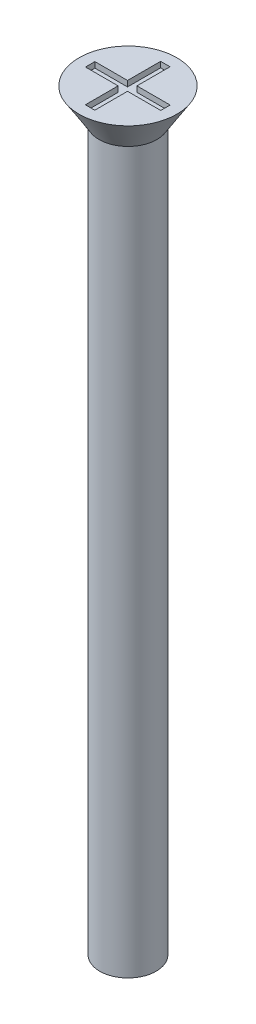
SolidWorks part; units mm, degrees
material "AISI 304"
ref_plane "Front" through (0, 0, 0) normal (0, 0, 1) x (1, 0, 0)
ref_plane "Top" through (0, 0, 0) normal (0, 1, 0) x (1, 0, 0)
ref_plane "Right" through (0, 0, 0) normal (1, 0, 0) x (0, 0, -1)
sketch "Sketch1" plane through (0, 0, 0) normal (0, 1, 0) x (1, 0, 0)
  circle A0 centre (0, 0) radius 1.5
  dimension "D1" = 3
extrude "Boss-Extrude1" add sketch "Sketch1" along normal blind 40
sketch "Sketch2" plane through (0, 40, 0) normal (0, 1, 0) x (1, 0, 0)
  circle A0 centre (0, 0) radius 2.6
  dimension "D1" = 5.2
extrude "Boss-Extrude2" add sketch "Sketch2" against normal blind 1.7 draft 32
sketch "Sketch3" plane through (0, 40, 0) normal (0, 1, 0) x (1, 0, 0)
  line L1 (-2, 0.2416) -> (2, 0.2416)
  line L2 (-2, 0.2416) -> (-2, -0.2584)
  line L3 (-2, -0.2584) -> (2, -0.2584)
  line L4 (2, 0.2416) -> (2, -0.2584)
  line L5 (-0.2653, 2) -> (0.2347, 2)
  line L6 (-0.2653, 2) -> (-0.2653, -2)
  line L7 (-0.2653, -2) -> (0.2347, -2)
  line L8 (0.2347, 2) -> (0.2347, -2)
  circle A0 centre (0, 0) radius 2.6 construction
  dimension "D1" = 0.5
  dimension "D2" = 0.5
  dimension "D3" = 4
  dimension "D4" = 4
  dimension "D5" = 2
  dimension "D6" = 2
extrude "Cut-Extrude1" cut sketch "Sketch3" against normal blind 0.3 contours L8 L5 L6 L1 | L8 L3 L6 L7 | L6 L1 L2 L3 | L1 L8 L3 L4 | L8 L1 L6 L3
